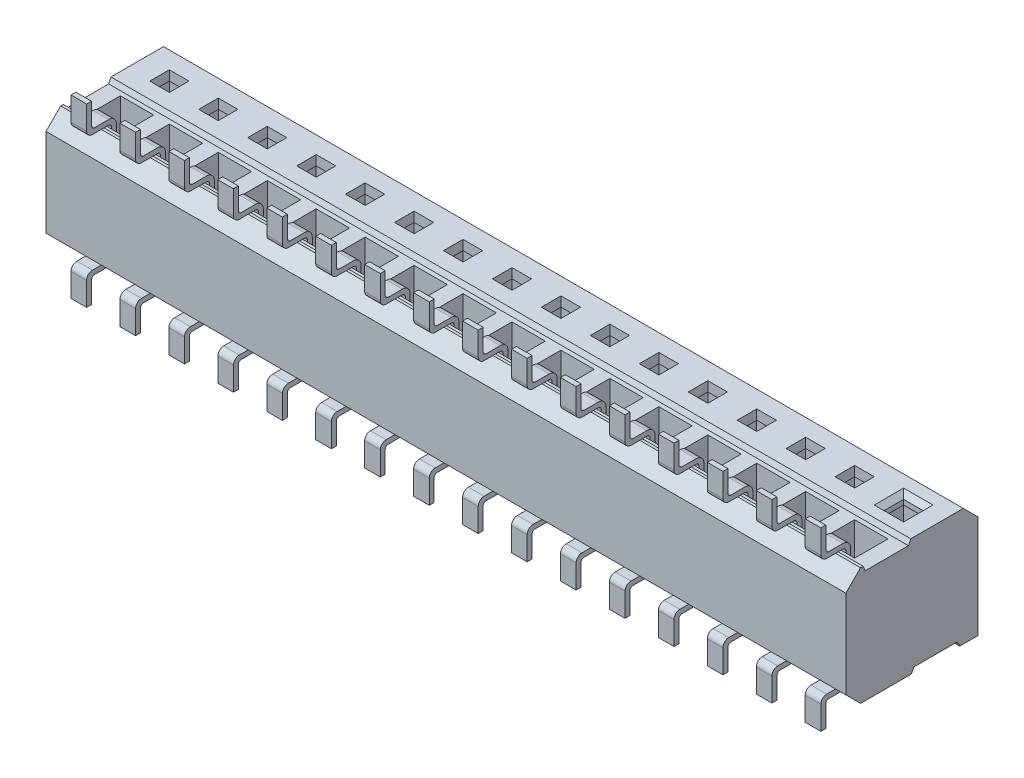
SolidWorks part; units mm, degrees
ref_plane "Front" through (0, 0, 0) normal (0, 0, 1) x (1, 0, 0)
ref_plane "Top" through (0, 0, 0) normal (0, 1, 0) x (1, 0, 0)
ref_plane "Right" through (0, 0, 0) normal (1, 0, 0) x (0, 0, -1)
sketch "Sketch1" plane through (0, 0, 0) normal (0, 1, 0) x (1, 0, 0)
  line L0 (-10.3759, -1.7145) -> (10.3759, 1.7145) construction
  line L1 (-10.3759, 1.7145) -> (10.3759, 1.7145)
  line L2 (-10.3759, 1.7145) -> (-10.3759, -1.7145)
  line L3 (-10.3759, -1.7145) -> (10.3759, -1.7145)
  line L4 (10.3759, 1.7145) -> (10.3759, -1.7145)
  dimension "D1" = 3.429
  dimension "D2" = 20.7518
extrude "Main Body" add sketch "Sketch1" along normal blind 3.048
ref_plane "Plane2" through (9.525, 0, 0) normal (1, 0, 0) x (0, 0, -1)
sketch "Sketch2" plane through (0, 3.048, 0) normal (0, 1, 0) x (-1, 0, 0)
  line L0 (0, 0) -> (-9.2157, 0) construction
  line L1 (-6.4241, -0.635) -> (-4.2326, -0.635) construction
  line L2 (-9.779, -0.381) -> (-9.271, -0.381)
  line L3 (-9.779, -0.381) -> (-9.779, -0.889)
  line L4 (-9.779, -0.889) -> (-9.271, -0.889)
  line L6 (-9.271, -0.381) -> (-9.271, -0.889)
  line L7 (-9.271, 0.381) -> (-9.271, 0.889)
  line L8 (-9.779, 0.889) -> (-9.271, 0.889)
  line L9 (-9.779, 0.381) -> (-9.779, 0.889)
  line L10 (-9.525, 1.9747) -> (-9.525, -2.1621) construction
  line L11 (-10.3759, 1.7145) -> (-10.3759, -1.7145) construction
  line L12 (-9.779, 0.381) -> (-9.271, 0.381)
  line L13 (-6.4241, 0.635) -> (-4.3872, 0.635) construction
  dimension "D1" = 1.27
  dimension "D2" = 0.508
  dimension "D3" = 0.508
  dimension "D4" = 0.8509
extrude "Cut-Extrude1" cut sketch "Sketch2" against normal blind 2.794
chamfer "Chamfer1" distance 0.127 distance2 0.127 8 edges at (9.779, 3.048, -0.635) (9.525, 3.048, -0.889) (9.271, 3.048, -0.635) (9.525, 3.048, -0.381) (9.525, 3.048, 0.381) (9.271, 3.048, 0.635) (9.525, 3.048, 0.889) (9.779, 3.048, 0.635)
sketch "Sketch6" plane through (10.3759, 0, 0) normal (1, 0, 0) x (0, 0, -1)
  line L1 (-1.7145, 3.048) -> (-1.7145, 0) construction
  line L2 (-1.7145, 0) -> (1.7145, 0) construction
  line L3 (-1.4097, 0) -> (1.4097, 0)
  line L5 (-1.4097, 0.127) -> (-1.4097, 0)
  line L7 (-1.4097, 0.127) -> (1.4097, 0.127)
  line L9 (1.4097, 0.127) -> (1.4097, 0)
  line L12 (1.7145, 3.048) -> (1.7145, 0) construction
  dimension "D2" = 0.3048
  dimension "D1" = 0.127
  dimension "D3" = 0.3048
sketch "Sketch7" plane through (9.525, 0, 0) normal (1, 0, 0) x (0, 0, -1)
  line L0 (0, 0) -> (0, 2.2434) construction
  line L1 (-0.889, 1.5621) -> (-0.889, 1.0541)
  line L2 (-1.143, 0.9271) -> (-2.159, 0.9271)
  line L3 (-0.889, 0.254) -> (-0.889, 2.921) construction
  line L4 (-1.016, 1.5621) -> (-1.016, 1.0541)
  line L5 (-2.159, 0.9271) -> (-2.159, 0.8001)
  line L6 (-1.143, 0.8001) -> (-2.159, 0.8001)
  line L7 (-1.7145, 3.048) -> (1.7145, 3.048) construction
  line L8 (-1.016, 1.5621) -> (-0.889, 1.5621)
  line L9 (1.016, 1.5621) -> (0.889, 1.5621)
  line L10 (1.143, 0.8001) -> (2.159, 0.8001)
  line L11 (2.159, 0.9271) -> (2.159, 0.8001)
  line L12 (1.016, 1.5621) -> (1.016, 1.0541)
  line L13 (1.143, 0.9271) -> (2.159, 0.9271)
  line L14 (0.889, 1.5621) -> (0.889, 1.0541)
  arc A0 (-0.889, 1.0541) -> (-1.143, 0.8001) centre (-1.143, 1.0541) cw
  arc A1 (-1.016, 1.0541) -> (-1.143, 0.9271) centre (-1.143, 1.0541) cw
  arc A2 (1.016, 1.0541) -> (1.143, 0.9271) centre (1.143, 1.0541) ccw
  arc A3 (0.889, 1.0541) -> (1.143, 0.8001) centre (1.143, 1.0541) ccw
  dimension "D2" = 0.254
  dimension "D1" = 2.2479
  dimension "D4" = 4.318
  dimension "D5" = 0.762
  dimension "D3" = 0.127
sketch "Sketch30" plane through (9.525, 0, 0) normal (1, 0, 0) x (0, 0, -1)
  line L0 (-1.7145, 3.048) -> (1.7145, 3.048) construction
  line L1 (-1.0668, 3.048) -> (-0.2032, 3.048)
  line L2 (-1.0668, 3.048) -> (-1.0668, 0.254)
  line L3 (-1.0668, 0.254) -> (-0.2032, 0.254)
  line L4 (-0.2032, 3.048) -> (-0.2032, 0.254)
  line L5 (-1.7145, 0) -> (1.7145, 0) construction
  line L6 (0.2032, 0) -> (1.0668, 0)
  line L7 (0.2032, 0) -> (0.2032, 2.794)
  line L8 (0.2032, 2.794) -> (1.0668, 2.794)
  line L9 (1.0668, 0) -> (1.0668, 2.794)
  line L10 (-0.635, 0.254) -> (-0.635, 1.4535) construction
  line L12 (0.635, 2.794) -> (0.635, 2.0625) construction
  line L14 (0, 0) -> (0, 3.8542) construction
  point P14 (0, 0)
  dimension "D1" = 0.254
  dimension "D3" = 0.8636
  dimension "D4" = 1.27
  dimension "D5" = 0.8636
  dimension "D6" = 0.254
extrude "Pin Cut-DH" cut sketch "Sketch30" against normal mid plane 0.8636
sketch "Sketch10" plane through (10.3759, 0, 0) normal (1, 0, 0) x (0, 0, -1)
  line L0 (0, 3.5147) -> (0, -0.2313) construction
  line L1 (-1.7373, 1.524) -> (1.6711, 1.524) construction
  line L2 (-1.7145, 3.048) -> (-1.3335, 3.048)
  line L3 (-1.7145, 3.048) -> (1.7145, 3.048) construction
  line L4 (-1.2649, 3.048) -> (-0.0305, 3.048)
  line L5 (-1.7145, 3.048) -> (-1.7145, 2.667)
  line L6 (-1.7145, 2.667) -> (-1.3335, 3.048)
  line L7 (1.7145, 2.667) -> (1.3335, 3.048)
  line L8 (-1.7145, 0) -> (1.7145, 0) construction
  line L9 (1.7145, 3.048) -> (1.7145, 2.667)
  line L10 (1.7145, 3.048) -> (1.3335, 3.048)
  line L11 (-1.7145, 0.381) -> (-1.3335, 0)
  line L12 (-1.7145, 0) -> (-1.7145, 0.381)
  line L13 (-1.7145, 0) -> (-1.3335, 0)
  line L14 (-0.0305, 3.048) -> (-0.0889, 2.921)
  line L15 (-0.0889, 2.921) -> (-1.2065, 2.921)
  line L16 (-1.2065, 2.921) -> (-1.2649, 3.048)
  line L17 (-0.0152, 0) -> (0.0533, 0.127)
  line L18 (0.0533, 0.127) -> (1.1709, 0.127)
  line L19 (1.1709, 0.127) -> (1.2395, 0)
  line L20 (-0.0152, 0) -> (1.2395, 0)
  line L21 (-0.6477, 2.921) -> (-0.6477, 2.4488) construction
  line L22 (1.7145, 3.048) -> (1.7145, 0) construction
  line L23 (0.6121, 0.127) -> (0.6121, 0.4568) construction
  dimension "D2" = 0.381
  dimension "D3" = 0.0686
  dimension "D1" = 0.381
  dimension "D4" = 0.127
  dimension "D5" = 0.0584
  dimension "D6" = 1.1176
  dimension "D7" = 0.127
  dimension "D8" = 1.1176
  dimension "D9" = 0.0686
  dimension "D10" = 0.475
extrude "Body Cut-DH" cut sketch "Sketch10" against normal through all
pattern_linear "DH Cut Pattern" count 16 spacing 1.27 along (-1, 0, 0) of "Cut-Extrude1", "Pin Cut-DH"
sketch "Sketch11" plane through (9.525, 0, 0) normal (1, 0, 0) x (0, 0, -1)
  line L0 (-0.0305, 3.048) -> (1.3335, 3.048) construction
  line L1 (-1.0668, 2.921) -> (-1.0668, 0.254) construction
  line L2 (-1.5621, 3.048) -> (-1.143, 3.048)
  line L3 (-1.7145, 2.667) -> (-1.7145, 0.381) construction
  line L4 (-1.7145, 3.81) -> (-1.7145, 3.2004)
  line L5 (-1.0668, 2.9718) -> (-1.0668, 2.4867)
  line L6 (-1.3335, 0) -> (-0.0152, 0) construction
  line L8 (-0.9398, 2.9718) -> (-0.9398, 2.4867)
  line L9 (-1.5113, 3.175) -> (-1.143, 3.175)
  line L10 (-1.5875, 3.81) -> (-1.5875, 3.2512)
  line L11 (-1.0668, 2.4867) -> (-0.9398, 2.4867)
  line L12 (-1.7145, 3.81) -> (-1.5875, 3.81)
  line L13 (0.2032, 0.6865) -> (0.2032, 0.0762)
  line L15 (-1.5621, 0) -> (0.127, 0)
  line L16 (-1.5875, -0.2032) -> (-1.5875, -0.762)
  line L17 (-1.7145, -0.1524) -> (-1.7145, -0.762)
  line L18 (0.3302, 0.6865) -> (0.3302, 0.0762)
  line L19 (-1.5113, -0.127) -> (0.127, -0.127)
  line L20 (-1.7145, -0.762) -> (-1.5875, -0.762)
  line L21 (0.2032, 0.6865) -> (0.3302, 0.6865)
  line L24 (0.2032, 2.794) -> (0.2032, 0.127) construction
  arc A0 (-1.0668, 2.9718) -> (-1.143, 3.048) centre (-1.143, 2.9718) ccw
  arc A1 (-1.5621, 3.048) -> (-1.7145, 3.2004) centre (-1.5621, 3.2004) cw
  arc A2 (-0.9398, 2.9718) -> (-1.143, 3.175) centre (-1.143, 2.9718) ccw
  arc A3 (-1.5621, 0) -> (-1.7145, -0.1524) centre (-1.5621, -0.1524) ccw
  arc A4 (0.2032, 0.0762) -> (0.127, 0) centre (0.127, 0.0762) cw
  arc A5 (0.3302, 0.0762) -> (0.127, -0.127) centre (0.127, 0.0762) cw
  arc A6 (-1.5113, -0.127) -> (-1.5875, -0.2032) centre (-1.5113, -0.2032) ccw
  arc A7 (-1.5113, 3.175) -> (-1.5875, 3.2512) centre (-1.5113, 3.2512) cw
  dimension "D1" = 0.0762
  dimension "D5" = 0.762
  dimension "D8" = 0.1524
  dimension "D7" = 0.0762
  dimension "D9" = 0.0762
  dimension "D12" = 0.2032
  dimension "D13" = 0.0762
  dimension "D14" = 0.1524
  dimension "D3" = 0.127
  dimension "D4" = 0.127
  dimension "D10" = 0.762
  dimension "D11" = 0.8135
  dimension "D15" = 0.6883
  dimension "D6" = 0.127
extrude "Lead Pin-DH" add sketch "Sketch11" along normal mid plane 0.4064
pattern_linear "Lead Pattern-DH" count 16 spacing 1.27 along (-1, 0, 0) of "Lead Pin-DH"
